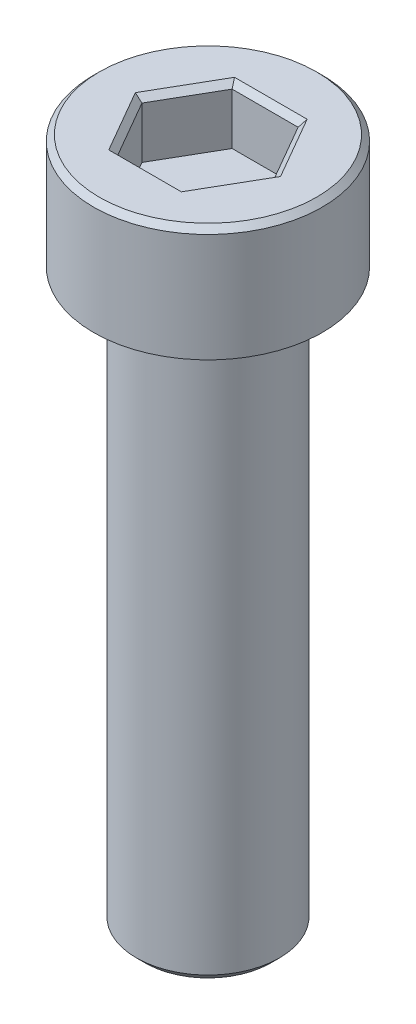
SolidWorks part; units mm, degrees
ref_plane "前视基准面" through (0, 0, 0) normal (0, 0, 1) x (1, 0, 0)
ref_plane "上视基准面" through (0, 0, 0) normal (0, 1, 0) x (1, 0, 0)
ref_plane "右视基准面" through (0, 0, 0) normal (1, 0, 0) x (0, 0, -1)
sketch "草图1" plane through (0, 0, 0) normal (0, 1, 0) x (1, 0, 0)
  circle A0 centre (0, 0) radius 4
  dimension "D1" = 8
extrude "凸台-拉伸1" add sketch "草图1" along normal blind 4
sketch "草图2" plane through (0, 0, 0) normal (0, -1, 0) x (1, 0, 0)
  circle A0 centre (0, 0) radius 2.5
  dimension "D1" = 5
extrude "凸台-拉伸2" add sketch "草图2" along normal blind 20
sketch "草图11" plane through (0, 4, 0) normal (0, 1, 0) x (1, 0, 0)
  line L1 (1.155, 1.9999) -> (-1.1544, 2.0001)
  line L2 (-1.1544, 2.0001) -> (-2.3094, 0.0003)
  line L3 (-2.3094, 0.0003) -> (-1.155, -1.9999)
  line L4 (-1.155, -1.9999) -> (1.1544, -2.0001)
  line L5 (1.1544, -2.0001) -> (2.3094, -0.0003)
  line L6 (2.3094, -0.0003) -> (1.155, 1.9999)
  circle A0 centre (0, 0) radius 2 construction
  dimension "D1" = 4
extrude "切除-拉伸1" cut sketch "草图11" against normal blind 2
chamfer "倒角1" distance 0.2 angle 45 7 edges at (0, 4, 4) (0.0003, 4, -2) (-1.7319, 4, -1.0002) (-1.7322, 4, 0.9998) (-0.0003, 4, 2) (1.7319, 4, 1.0002) (1.7322, 4, -0.9998)
chamfer "倒角2" distance 0.3 angle 45 1 edges at (0, -20, -2.5)
